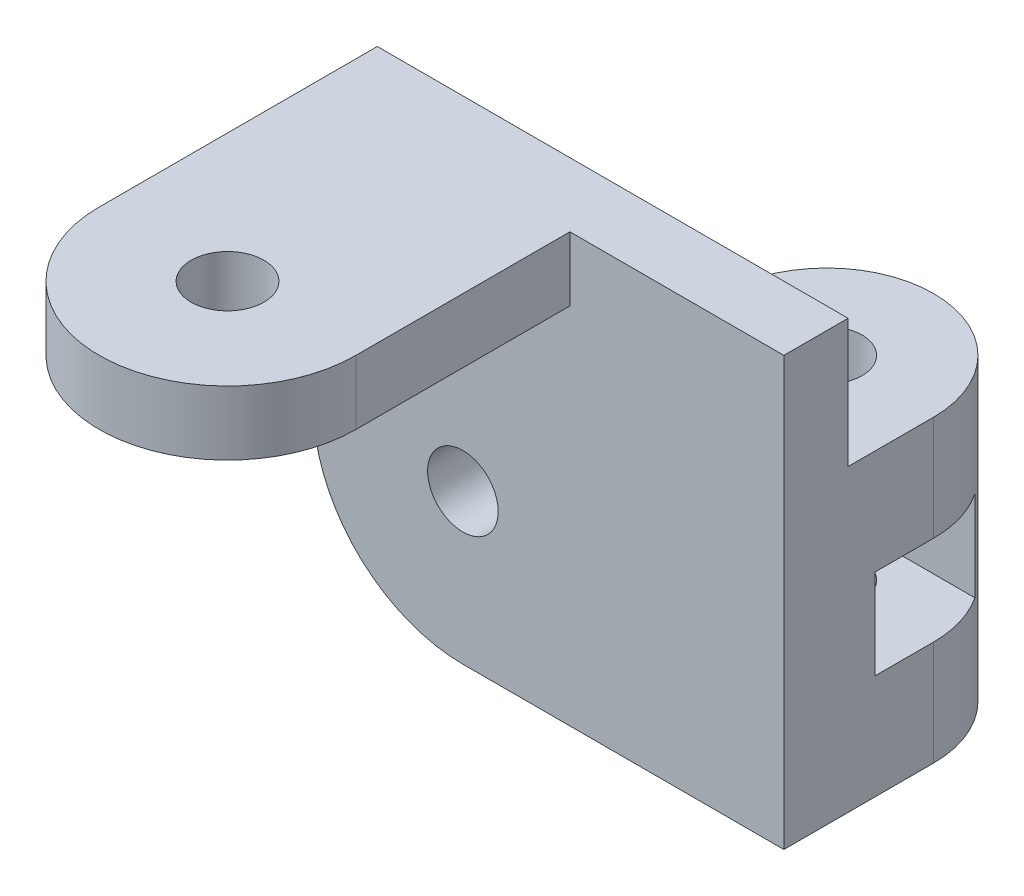
SolidWorks part; units mm, degrees
ref_plane "Plano frontal" through (0, 0, 0) normal (0, 0, 1) x (1, 0, 0)
ref_plane "Plano superior" through (0, 0, 0) normal (0, 1, 0) x (1, 0, 0)
ref_plane "Plano direito" through (0, 0, 0) normal (1, 0, 0) x (0, 0, -1)
sketch "Esboço1" plane through (0, 0, 0) normal (0, 0, 1) x (1, 0, 0)
  line L0 (-2.5, 0) -> (2.5, 0) construction
  line L2 (-2.5, -7) -> (2.5, -7)
  line L4 (12.5, 13) -> (12.5, -7)
  line L5 (12.5, -7) -> (2.5, -7)
  line L6 (-9.5, 0) -> (-9.5, 13)
  line L7 (-9.5, 13) -> (12.5, 13)
  arc A0 (-9.5, 0) -> (-2.5, -7) centre (-2.5, 0) ccw
  circle A3 centre (-2.5, 0) radius 1.65
  point P3 (0, 0)
  dimension "D1" = 7
  dimension "D4" = 13
  dimension "D2" = 5
  dimension "D3" = 15
extrude "Ressalto-extrusão1" add sketch "Esboço1" along normal blind 3
sketch "Esboço3" plane through (0, -7, 0) normal (0, 1, 0) x (1, 0, 0)
  line L1 (2.5, 4) -> (2.5, 0)
  line L2 (2.5, 0) -> (12.5, 0)
  line L3 (12.5, 0) -> (12.5, 4)
  circle A0 centre (7.5, 4) radius 1.65
  arc A1 (12.5, 4) -> (2.5, 4) centre (7.5, 4) ccw
  dimension "D1" = 3.3
  dimension "D2" = 5
  dimension "D3" = 4
extrude "Ressalto-extrusão2" add sketch "Esboço3" along normal blind 14
sketch "Esboço4" plane through (12.5, 0, 0) normal (1, 0, 0) x (0, 0, -1)
  line L0 (4, 7) -> (4, -7) construction
  line L1 (6.75, 2.1) -> (1.25, 2.1)
  line L2 (6.75, 2.1) -> (6.75, -2.1)
  line L3 (6.75, -2.1) -> (1.25, -2.1)
  line L4 (1.25, 2.1) -> (1.25, -2.1)
  line L5 (0, 0) -> (10.3549, 0) construction
  line L8 (4, 7) -> (4, -7) construction
  dimension "D1" = 4.2
  dimension "D2" = 5.5
extrude "Corte-extrusão1" cut sketch "Esboço4" against normal blind 10
sketch "Esboço5" plane through (0, 13, 0) normal (0, 1, 0) x (1, 0, 0)
  line L0 (2.5, 0) -> (2.5, -13)
  line L1 (-9.5, -13) -> (-9.5, 0)
  line L2 (-9.5, 0) -> (2.5, 0)
  line L3 (12.5, -3) -> (-9.5, -3) construction
  circle A0 centre (-3.5, -13) radius 1.7
  arc A1 (2.5, -13) -> (-9.5, -13) centre (-3.5, -13) cw
  dimension "D2" = 3.4
  dimension "D1" = 10
extrude "Ressalto-extrusão3" add sketch "Esboço5" against normal blind 3
